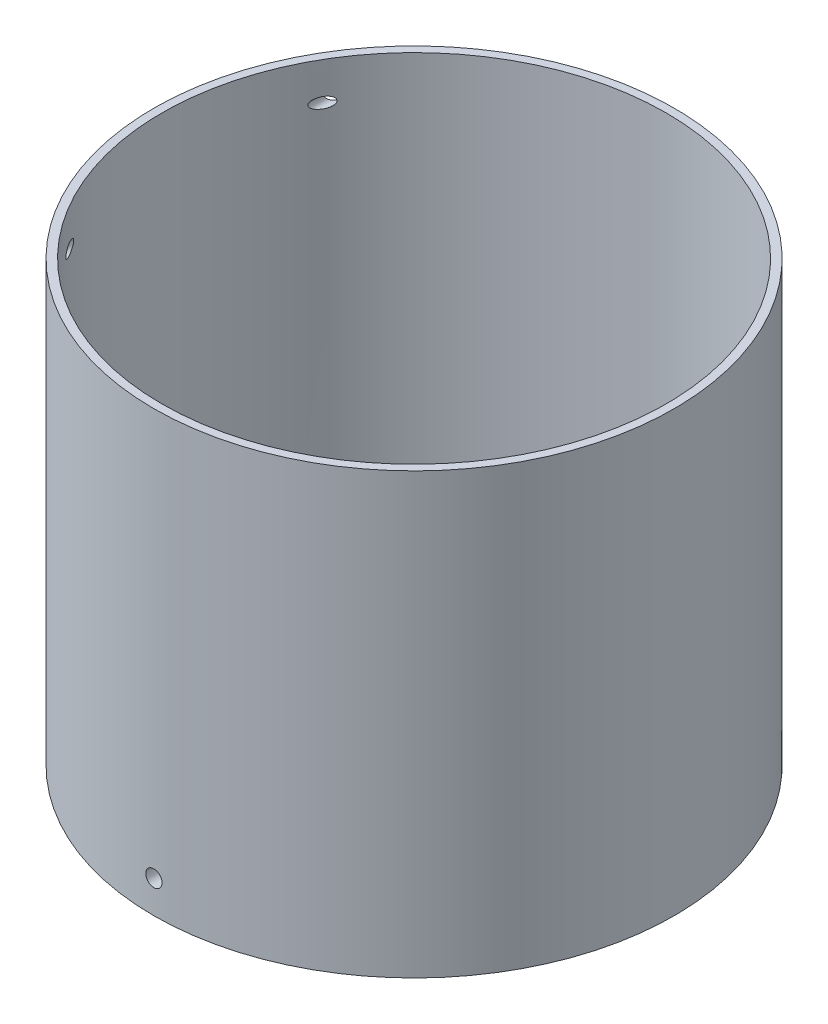
SolidWorks part; units mm, degrees
material "6061-T6 (SS)"
ref_plane "Front Plane" through (0, 0, 0) normal (0, 0, 1) x (1, 0, 0)
ref_plane "Top Plane" through (0, 0, 0) normal (0, 1, 0) x (1, 0, 0)
ref_plane "Right Plane" through (0, 0, 0) normal (1, 0, 0) x (0, 0, -1)
sketch "Sketch1" plane through (0, 0, 0) normal (0, 1, 0) x (1, 0, 0)
  circle A0 centre (0, 0) radius 101.6
  circle A1 centre (0, 0) radius 95.25
  dimension "D1" = 203.2
  dimension "D2" = 190.5
extrude "Boss-Extrude1" add sketch "Sketch1" along normal blind 25.4
sketch "Sketch2" plane through (0, 0, 0) normal (0, 0, 1) x (1, 0, 0)
  circle A0 centre (0, 12.7) radius 3.175
  dimension "D1" = 6.35
extrude "Cut-Extrude1" cut sketch "Sketch2" against normal through all and the other way through all
sketch "Sketch3" plane through (0, 0, 0) normal (1, 0, 0) x (0, 0, -1)
  circle A0 centre (0, 12.7) radius 1.5875
  dimension "D1" = 3.175
extrude "Cut-Extrude3" [suppressed] cut sketch "Sketch3" against normal through all
sketch "Sketch4" plane through (0, 0, 0) normal (1, 0, 0) x (0, 0, -1)
  line L0 (0, 0) -> (0, 72.5565) construction
pattern_circular "CirPattern1" [suppressed] count 24 over 360 about axis through (0, 0, 0) along (0, 1, 0)
sketch "Sketch5" plane through (0, 25.4, 0) normal (0, 1, 0) x (1, 0, 0)
  circle A0 centre (0, 0) radius 98.425
  circle A1 centre (0, 0) radius 101.6
extrude "Boss-Extrude2" add sketch "Sketch5" along normal blind 146.05
sketch "Sketch6" plane through (0, 0, 0) normal (0, -1, 0) x (1, 0, 0)
  circle A0 centre (0, 0) radius 101.6
  circle A1 centre (0, 0) radius 98.425
extrude "Boss-Extrude3" [suppressed] add sketch "Sketch6" along normal blind 133.35
ref_plane "Plane1" through (0, 0, 101.6) normal (0, 0, 1) x (1, 0, 0)
sketch "Sketch9" plane through (0, 0, 101.6) normal (0, 0, 1) x (1, 0, 0)
  line L0 (-101.6, 0) -> (101.6, 0) construction
  line L1 (0, 0) -> (0, 72.5565) construction
  circle A0 centre (-85.075, 156.8) radius 2.1
  dimension "D1" = 156.8
  dimension "D2" = 85.075
extrude "Cut-Extrude5" cut sketch "Sketch9" against normal through all
